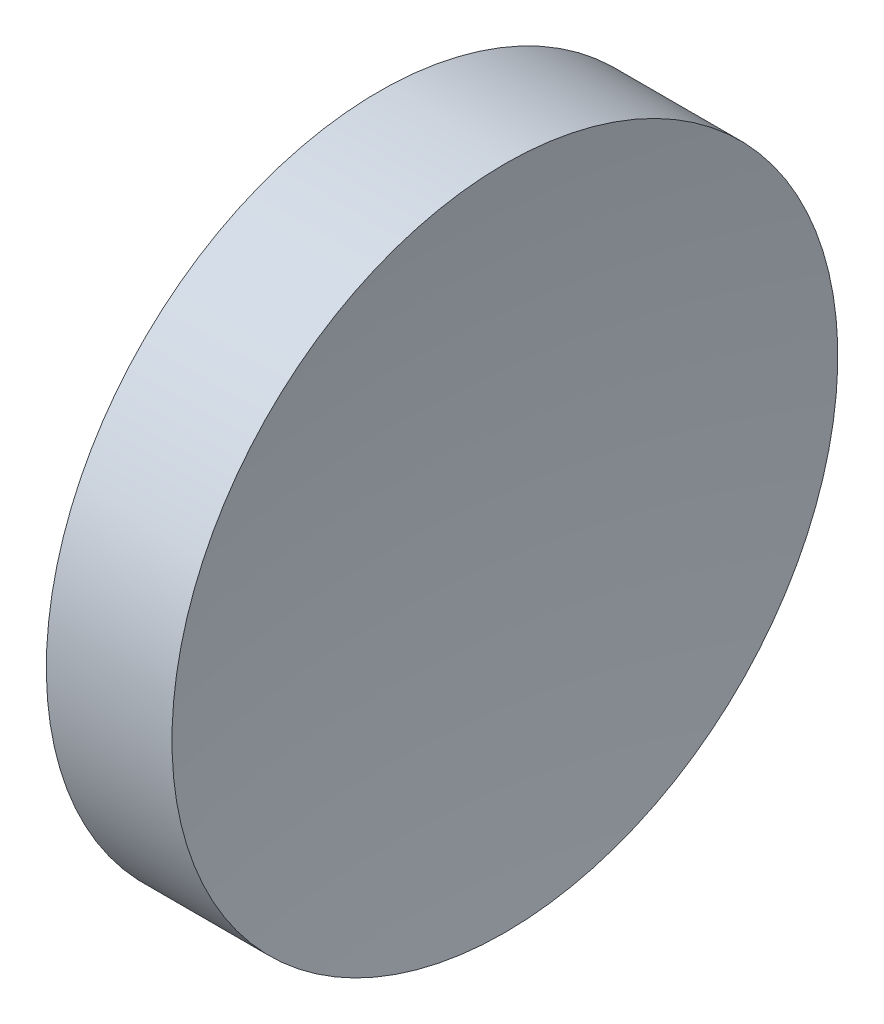
SolidWorks part; units mm, degrees
ref_plane "前视基准面" through (0, 0, 0) normal (0, 0, 1) x (1, 0, 0)
ref_plane "上视基准面" through (0, 0, 0) normal (0, 1, 0) x (1, 0, 0)
ref_plane "右视基准面" through (0, 0, 0) normal (1, 0, 0) x (0, 0, -1)
sketch "草图1" plane through (0, 0, 0) normal (0, 0, 1) x (1, 0, 0)
  line L0 (21.506, 13.0311) -> (26.997, 13.0311) construction
  line L1 (22.4242, 13.0311) -> (22.4242, 18.0311)
  line L2 (22.4242, 18.0311) -> (24.3112, 18.0311)
  line L3 (23.9242, 13.0311) -> (22.4242, 13.0311)
  arc A0 (24.3112, 18.0311) -> (23.9242, 13.0311) centre (56.4242, 13.0311) ccw
revolve "旋转1" add sketch "草图1" angle 360 about L0
